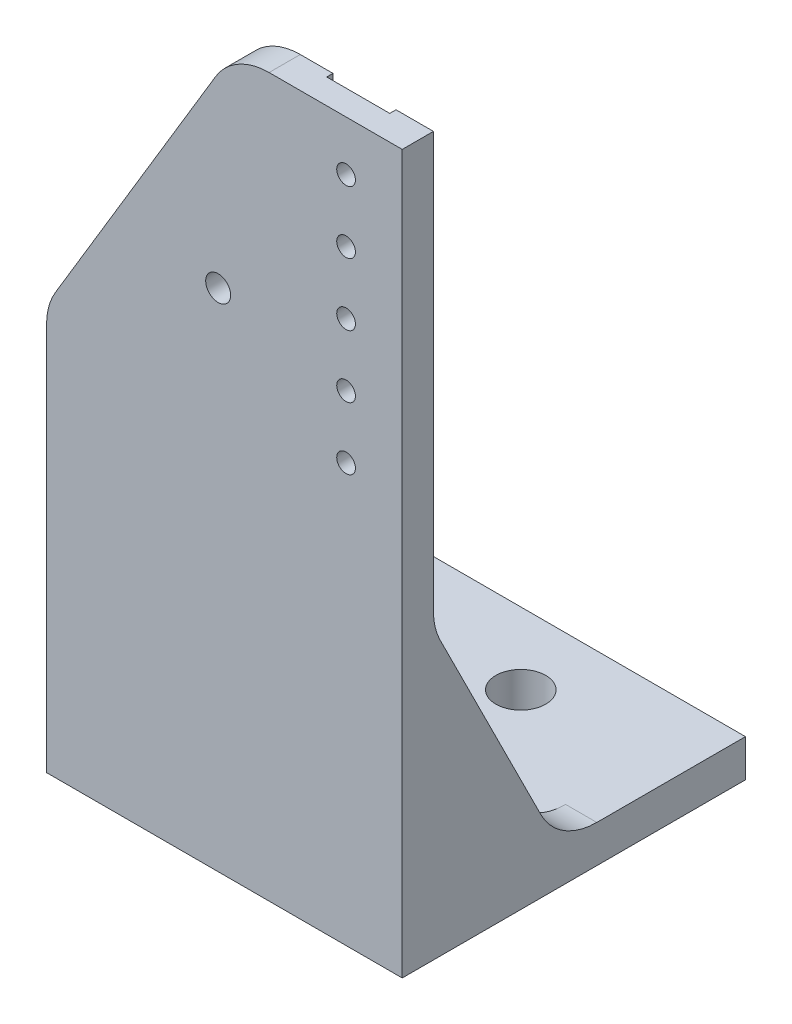
SolidWorks part; units mm, degrees
material "6061 合金"
ref_plane "前视基准面" through (0, 0, 0) normal (0, 0, 1) x (1, 0, 0)
ref_plane "上视基准面" through (0, 0, 0) normal (0, 1, 0) x (1, 0, 0)
ref_plane "右视基准面" through (0, 0, 0) normal (1, 0, 0) x (0, 0, -1)
sketch "草图1" plane through (0, 0, 0) normal (0, 1, 0) x (1, 0, 0)
  line L0 (0, 0) -> (0, -10)
  line L1 (0, -10) -> (40, -10)
  line L2 (40, -10) -> (40, 0)
  line L3 (40, 0) -> (0, 0)
  line L4 (0, 0) -> (0, 15)
  line L5 (0, 15) -> (40, 15)
  line L6 (40, 15) -> (40, 0)
  line L7 (0, -10) -> (0, -20)
  line L8 (0, -20) -> (40, -20)
  line L9 (40, -20) -> (40, -10)
  line L10 (0, 15) -> (-20, 15)
  line L11 (-20, 15) -> (-20, -20)
  line L12 (-20, -20) -> (0, -20)
  line L13 (40, 15) -> (45, 15)
  line L14 (45, 15) -> (45, -20)
  line L15 (45, -20) -> (40, -20)
extrude "凸台-拉伸1" add sketch "草图1" along normal blind 6 contours L2 L3 L0 L1 | L6 L5 L4 L3 | L8 L9 L1 L7 | L11 L12 L7 L0 L4 L10 | L15 L14 L13 L6 L2 L9
sketch "草图3" plane through (0, 6, 0) normal (0, 1, 0) x (1, 0, 0)
  line L0 (-20, -20) -> (-20, -6.5)
  line L1 (12.5, -6.5) -> (-12.5, -6.5)
  line L2 (-20, 15) -> (-20, -20) construction
  line L3 (-20, -6.5) -> (45, -6.5)
  line L6 (45, 15) -> (45, -20) construction
  line L7 (-12.5, -6.5) -> (37.5, -6.5)
  circle A3 centre (12.5, -6.5) radius 3
  circle A4 centre (-12.5, -6.5) radius 4
  point P11 (12.5418, -2.5)
  point P13 (12.5, -6.5)
extrude "切除-拉伸1" cut sketch "草图3" against normal through all
sketch "草图4" plane through (0, 6, 0) normal (0, 1, 0) x (1, 0, 0)
  line L10 (12.5, -6.5) -> (6.5, -6.5)
  line L11 (12.5, -6.5) -> (12.5, -19)
  line L12 (12.5, -19) -> (6.5, -19)
  line L13 (6.5, -19) -> (6.5, 7)
  line L14 (6.5, 7) -> (21.5, 7)
  line L15 (21.5, 7) -> (21.5, -19)
  line L16 (21.5, -19) -> (12.5, -19)
  circle M13 centre (12.5, -6.5) radius 3
extrude "切除-拉伸2" cut sketch "草图4" against normal blind 1 contours L16 L15 L14 L13 L10 L11 M13 | L13 L12 L11 L10 M13
sketch "草图6" plane through (0, 0, 20) normal (0, 0, 1) x (1, 0, 0)
  line L0 (12.5, 6) -> (12.5, 81)
  line L1 (-20, 6) -> (45, 6) construction
  line L2 (12.5, 6) -> (12.5, 0)
  line L3 (-20, 0) -> (45, 0) construction
  line L4 (12.5, 0) -> (-20, 0)
  line L5 (-20, 0) -> (-20, 115)
  line L6 (-20, 115) -> (45, 115)
  line L7 (45, 115) -> (45, 0)
  line L8 (45, 0) -> (12.5, 0)
  line L9 (12.5, 81) -> (7.5, 81)
  circle A0 centre (12.5, 81) radius 2
  circle A1 centre (7.5, 81) radius 2
extrude "凸台-拉伸2" add sketch "草图6" along normal blind 5
sketch "草图7" plane through (0, 0, 20) normal (0, 0, -1) x (-1, 0, 0)
  line L1 (20, 115) -> (-45, 115) construction
  line L2 (-28, 115) -> (-28, 87)
  line L3 (-45, 115) -> (-28, 115)
  circle A3 centre (-28, 87) radius 1.5
extrude "切除-拉伸4" cut sketch "草图7" against normal through all
sketch "草图8" plane through (0, 0, 20) normal (0, 0, -1) x (-1, 0, 0)
  line L0 (-31, 60) -> (-31, 115)
  line L1 (20, 115) -> (-45, 115) construction
  line L2 (-31, 115) -> (-20.9, 115)
  line L3 (-20.9, 115) -> (-20.9, 60)
  line L4 (-20.9, 60) -> (-31, 60)
  line L5 (-45, 115) -> (-31, 115)
  line M4 (20, 115) -> (-45, 115)
  circle M17 centre (-28, 87) radius 1.5
extrude "切除-拉伸5" cut sketch "草图8" against normal blind 1 contours L4 L3 L0 M4 M17
sketch "草图9" plane through (0, 0, 0) normal (0, -1, 0) x (1, 0, 0)
  circle A1 centre (12.5, 6.5) radius 6
extrude "切除-拉伸6" cut sketch "草图9" against normal blind 2
sketch "草图10" plane through (0, 0, 0) normal (0, -1, 0) x (1, 0, 0)
  line L0 (-20, -15) -> (-20, -30)
  line L1 (-20, -30) -> (45, -30)
  line L2 (45, -30) -> (45, -15)
  line L3 (45, -15) -> (-20, -15)
extrude "凸台-拉伸3" add sketch "草图10" against normal blind 6
sketch "草图11" plane through (0, 6, 0) normal (0, 1, 0) x (1, 0, 0)
  line L0 (12.5, -6.5) -> (12.5, 18.5)
  circle A0 centre (12.5, 18.5) radius 4
extrude "切除-拉伸7" cut sketch "草图11" against normal blind 6 contours A0
sketch "草图12" plane through (45, 0, 0) normal (1, 0, 0) x (0, 0, -1)
  line L1 (-121.3567, 195.2896) -> (40.6098, 195.2896)
  line L2 (-121.3567, 195.2896) -> (-121.3567, -4.5543)
  line L3 (-121.3567, -4.5543) -> (40.6098, -4.5543)
  line L4 (40.6098, 195.2896) -> (40.6098, -4.5543)
  line L5 (-121.3567, 195.2896) -> (40.6098, -4.5543) construction
  line L6 (-121.3567, -4.5543) -> (40.6098, 195.2896) construction
  point P0 (-40.3735, 95.3676)
extrude "切除-拉伸8" cut sketch "草图12" against normal blind 8
pattern_linear "阵列(线性)1" count 3 spacing 10 along (0, -1, 0) count 3 spacing 10 along (0, 1, 0) of "切除-拉伸4"
chamfer "倒角1" distance 30 distance2 50 1 edges at (-20, 115, 22.5)
fillet "圆角1" radius 10 2 edges at (-20, 65, 22.5) (10, 115, 22.5)
sketch "草图13" plane through (37, 0, 0) normal (1, 0, 0) x (0, 0, -1)
  line L0 (-20, 6) -> (0, 6)
  line L1 (-20, 6) -> (30, 6) construction
  line L2 (-20, 6) -> (-20, 46)
  line L3 (-20, 6) -> (-20, 115) construction
  line L4 (-20, 46) -> (0, 6)
extrude "凸台-拉伸4" add sketch "草图13" against normal blind 5
fillet "圆角2" radius 10 2 edges at (34.5, 6, 0) (34.5, 46, 20)
ref_plane "基准面1" through (-20, 6, -30) normal (1, 0, 0) x (0, 0, -1)
